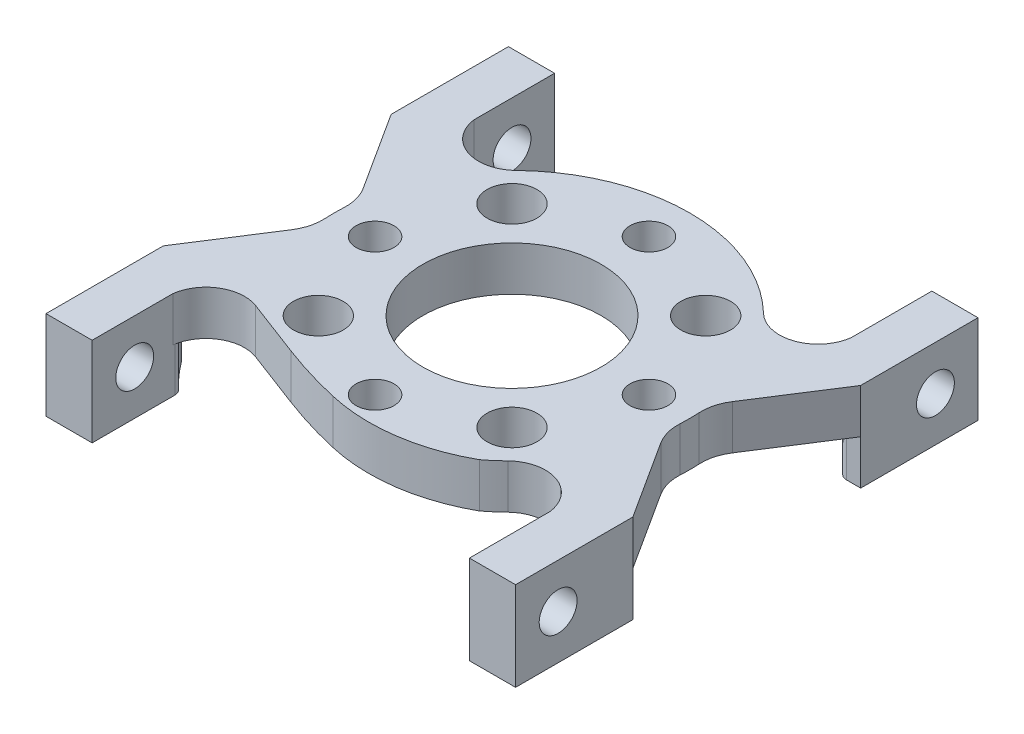
SolidWorks part; units mm, degrees
ref_plane "Front Plane" through (0, 0, 0) normal (0, 0, 1) x (1, 0, 0)
ref_plane "Top Plane" through (0, 0, 0) normal (0, 1, 0) x (1, 0, 0)
ref_plane "Right Plane" through (0, 0, 0) normal (1, 0, 0) x (0, 0, -1)
ref_plane "Plane1" through (0, 0, 0) normal (0, -1, 0) x (1, 0, 0)
sketch "Sketch1" plane through (0, 0, 0) normal (0, -1, 0) x (1, 0, 0)
  line L0 (16.764, 16.51) -> (-16.764, 16.51)
  line L1 (-16.764, 16.51) -> (-16.764, -16.51)
  line L2 (-16.764, -16.51) -> (16.764, -16.51)
  line L3 (16.764, -16.51) -> (16.764, 16.51)
extrude "Boss-Extrude1" add sketch "Sketch1" against normal blind 3.175
sketch "Sketch2" plane through (0, 3.175, 0) normal (0, 1, 0) x (-1, 0, 0)
  line L0 (-13.4696, 16.51) -> (-13.4696, 10.7533)
  line L1 (13.4696, 10.7533) -> (13.4696, 16.51)
  line L2 (13.4696, 16.51) -> (-13.4696, 16.51)
  arc A0 (-13.4696, 10.7533) -> (-8.8308, 9.1273) centre (-10.7425, 11.1033) ccw
  arc A1 (-8.8308, 9.1273) -> (8.8308, 9.1273) centre (0, 0) cw
  arc A2 (8.8308, 9.1273) -> (13.4696, 10.7533) centre (10.7425, 11.1033) ccw
extrude "Cut-Extrude1" cut sketch "Sketch2" against normal through all
sketch "Sketch3" plane through (0, 0, 0) normal (0, -1, 0) x (1, 0, 0)
  line L0 (-13.4696, 8.1331) -> (-16.764, 8.1331)
  line L1 (-16.764, 8.1331) -> (-16.764, 16.51)
  line L2 (-16.764, 16.51) -> (-13.4696, 16.51)
  line L3 (-13.4696, 16.51) -> (-13.4696, 8.1331)
extrude "Boss-Extrude2" add sketch "Sketch3" along normal blind 3.175
sketch "Sketch4" plane through (0, 3.175, 0) normal (0, 1, 0) x (-1, 0, 0)
  line L0 (-16.764, 8.1331) -> (-16.764, -8.1331)
  line L1 (-16.764, -8.1331) -> (-12.5937, -1.6399)
  line L2 (-12.5937, 1.6399) -> (-16.764, 8.1331)
  arc A0 (-12.5937, -1.6399) -> (-12.5937, 1.6399) centre (0, 0) cw
extrude "Cut-Extrude2" cut sketch "Sketch4" against normal through all
sketch "Sketch5" plane through (0, 0, 0) normal (0, -1, 0) x (1, 0, 0)
  line L0 (13.4696, 8.1331) -> (13.4696, 16.51)
  line L1 (13.4696, 16.51) -> (16.764, 16.51)
  line L2 (16.764, 16.51) -> (16.764, 8.1331)
  line L3 (16.764, 8.1331) -> (13.4696, 8.1331)
extrude "Boss-Extrude3" add sketch "Sketch5" along normal blind 3.175
sketch "Sketch6" plane through (0, 3.175, 0) normal (0, 1, 0) x (-1, 0, 0)
  line L0 (13.4696, -16.51) -> (13.4696, -10.7533)
  line L1 (-13.4696, -10.7533) -> (-13.4696, -16.51)
  line L2 (-13.4696, -16.51) -> (13.4696, -16.51)
  arc A0 (13.4696, -10.7533) -> (8.8308, -9.1273) centre (10.7425, -11.1033) ccw
  arc A1 (8.8308, -9.1273) -> (-8.8308, -9.1273) centre (0, 0) cw
  arc A2 (-8.8308, -9.1273) -> (-13.4696, -10.7533) centre (-10.7425, -11.1033) ccw
extrude "Cut-Extrude3" cut sketch "Sketch6" against normal through all
sketch "Sketch7" plane through (0, 0, 0) normal (0, -1, 0) x (1, 0, 0)
  line L0 (13.4696, -8.1331) -> (16.764, -8.1331)
  line L1 (16.764, -8.1331) -> (16.764, -16.51)
  line L2 (16.764, -16.51) -> (13.4696, -16.51)
  line L3 (13.4696, -16.51) -> (13.4696, -8.1331)
extrude "Boss-Extrude4" add sketch "Sketch7" along normal blind 3.175
sketch "Sketch8" plane through (0, 3.175, 0) normal (0, 1, 0) x (-1, 0, 0)
  line L0 (16.764, -8.1331) -> (16.764, 8.1331)
  line L1 (16.764, 8.1331) -> (12.5937, 1.6399)
  line L2 (12.5937, -1.6399) -> (16.764, -8.1331)
  arc A0 (12.5937, 1.6399) -> (12.5937, -1.6399) centre (0, 0) cw
extrude "Cut-Extrude4" cut sketch "Sketch8" against normal through all
sketch "Sketch9" plane through (0, 0, 0) normal (0, -1, 0) x (1, 0, 0)
  line L0 (-13.4696, -8.1331) -> (-13.4696, -16.51)
  line L1 (-13.4696, -16.51) -> (-16.764, -16.51)
  line L2 (-16.764, -16.51) -> (-16.764, -8.1331)
  line L3 (-16.764, -8.1331) -> (-13.4696, -8.1331)
extrude "Boss-Extrude5" add sketch "Sketch9" along normal blind 3.175
sketch "Sketch10" plane through (0, -3.175, 0) normal (0, -1, 0) x (1, 0, 0)
  line L0 (15.4224, -8.1331) -> (13.4696, -8.1331)
  line L1 (13.4696, -8.1331) -> (13.4696, -10.3293)
  arc A0 (13.4696, -10.3293) -> (15.4224, -8.1331) centre (4.064, 0) ccw
extrude "Cut-Extrude5" cut sketch "Sketch10" against normal blind 3.175
sketch "Sketch11" plane through (0, -3.175, 0) normal (0, -1, 0) x (1, 0, 0)
  line L0 (13.4696, 10.3293) -> (13.4696, 8.1331)
  line L1 (13.4696, 8.1331) -> (15.4224, 8.1331)
  arc A0 (15.4224, 8.1331) -> (13.4696, 10.3293) centre (4.064, 0) ccw
extrude "Cut-Extrude6" cut sketch "Sketch11" against normal blind 3.175
sketch "Sketch12" plane through (0, -3.175, 0) normal (0, -1, 0) x (1, 0, 0)
  line L0 (-15.4224, 8.1331) -> (-13.4696, 8.1331)
  line L1 (-13.4696, 8.1331) -> (-13.4696, 10.3293)
  arc A0 (-13.4696, 10.3293) -> (-15.4224, 8.1331) centre (-4.064, 0) ccw
extrude "Cut-Extrude7" cut sketch "Sketch12" against normal blind 3.175
sketch "Sketch13" plane through (0, -3.175, 0) normal (0, -1, 0) x (1, 0, 0)
  line L0 (-13.4696, -10.3293) -> (-13.4696, -8.1331)
  line L1 (-13.4696, -8.1331) -> (-15.4224, -8.1331)
  arc A0 (-15.4224, -8.1331) -> (-13.4696, -10.3293) centre (-4.064, 0) ccw
extrude "Cut-Extrude8" cut sketch "Sketch13" against normal blind 3.175
hole_wizard "Hole1" positions "Sketch15" profile "Sketch14" legacy
sketch "Sketch15" plane through (0, 0, 0) normal (0, -1, 0) x (-1, 0, 0)
  point P0 (0, 0)
sketch "Sketch14" plane through (0, 0, 0) normal (1, 0, 0) x (0, 0, -1)
  line L0 (0, 0) -> (0, 3.175)
  line L1 (0, 3.175) -> (6.3627, 3.175)
  line L2 (6.3627, 3.175) -> (6.3627, 0)
  line L3 (6.3627, 0) -> (0, 0)
  line L4 (0, 110) -> (0, -10) construction
  dimension "Diameter" = 12.7254
  dimension "Depth" = 3.175
hole_wizard "M2.5 Clearance Hole1" positions "Sketch17" profile "Sketch16" hole size "M2.5" standard "ANSI Metric"
sketch "Sketch17" plane through (0, 0, 0) normal (0, -1, 0) x (-1, 0, 0)
  point P0 (0, -9.779)
  point P1 (9.779, 0)
  point P2 (0, 9.779)
  point P3 (-9.779, 0)
sketch "Sketch16" plane through (0, 0, 9.779) normal (1, 0, 0) x (0, 0, -1)
  line L0 (0, 0) -> (0, 3.175)
  line L1 (0, 3.175) -> (1.3525, 3.175)
  line L2 (1.3525, 3.175) -> (1.3525, 0)
  line L5 (1.3525, 0) -> (0, 0)
  line L11 (0, -6.35) -> (0, 107.95) construction
  dimension "Thru Hole Dia." = 2.7051
  dimension "Thru Hole Depth" = 3.175
hole_wizard "M3 Clearance Hole1" positions "Sketch19" profile "Sketch18" hole size "M3" standard "ANSI Metric"
sketch "Sketch19" plane through (0, 0, 0) normal (0, -1, 0) x (-1, 0, 0)
  point P0 (6.9148, -6.9148)
  point P1 (6.9148, 6.9148)
  point P2 (-6.9148, 6.9148)
  point P3 (-6.9148, -6.9148)
sketch "Sketch18" plane through (-6.9148, 0, 6.9148) normal (1, 0, 0) x (0, 0, -1)
  line L0 (0, 0) -> (0, 3.175)
  line L1 (0, 3.175) -> (1.778, 3.175)
  line L2 (1.778, 3.175) -> (1.778, 0)
  line L5 (1.778, 0) -> (0, 0)
  line L11 (0, -6.35) -> (0, 107.95) construction
  dimension "Thru Hole Dia." = 3.556
  dimension "Thru Hole Depth" = 3.175
hole_wizard "M2.5 Clearance Hole2" positions "Sketch21" profile "Sketch20" hole size "M2.5" standard "ANSI Metric"
sketch "Sketch21" plane through (16.764, 0, 0) normal (1, 0, 0) x (0, 0, -1)
  point P0 (13.4704, 0)
sketch "Sketch20" plane through (16.764, 0, -13.4704) normal (0, 1, 0) x (0, 0, -1)
  line L0 (0, 0) -> (0, 3.2944)
  line L1 (0, 3.2944) -> (1.3525, 3.2944)
  line L2 (1.3525, 3.2944) -> (1.3525, 0)
  line L5 (1.3525, 0) -> (0, 0)
  line L11 (0, -6.35) -> (0, 107.95) construction
  dimension "Thru Hole Dia." = 2.7051
  dimension "Thru Hole Depth" = 3.2944
hole_wizard "M2.5 Clearance Hole3" positions "Sketch23" profile "Sketch22" hole size "M2.5" standard "ANSI Metric"
sketch "Sketch23" plane through (13.4696, 0, 0) normal (-1, 0, 0) x (0, 0, 1)
  point P0 (13.4704, 0)
sketch "Sketch22" plane through (13.4696, 0, 13.4704) normal (0, 1, 0) x (0, 0, 1)
  line L0 (0, 0) -> (0, 3.2944)
  line L1 (0, 3.2944) -> (1.3525, 3.2944)
  line L2 (1.3525, 3.2944) -> (1.3525, 0)
  line L5 (1.3525, 0) -> (0, 0)
  line L11 (0, -6.35) -> (0, 107.95) construction
  dimension "Thru Hole Dia." = 2.7051
  dimension "Thru Hole Depth" = 3.2944
hole_wizard "M2.5 Clearance Hole4" positions "Sketch25" profile "Sketch24" hole size "M2.5" standard "ANSI Metric"
sketch "Sketch25" plane through (-13.4696, 0, 0) normal (1, 0, 0) x (0, 0, -1)
  point P0 (-13.4704, 0)
  point P1 (13.4704, 0)
sketch "Sketch24" plane through (-13.4696, 0, 13.4704) normal (0, 1, 0) x (0, 0, -1)
  line L0 (0, 0) -> (0, 3.2944)
  line L1 (0, 3.2944) -> (1.3525, 3.2944)
  line L2 (1.3525, 3.2944) -> (1.3525, 0)
  line L5 (1.3525, 0) -> (0, 0)
  line L11 (0, -6.35) -> (0, 107.95) construction
  dimension "Thru Hole Dia." = 2.7051
  dimension "Thru Hole Depth" = 3.2944
fillet "Fillet1" radius 0.635 8 edges at (-13.4696, -1.5875, -10.3293) (-15.4224, -1.5875, 8.1331) (15.4224, -1.5875, -8.1331) (15.4224, -1.5875, 8.1331) (13.4696, -1.5875, -10.3293) (-13.4696, -1.5875, 10.3293) (-15.4224, -1.5875, -8.1331) (13.4696, -1.5875, 10.3293)
fillet "Fillet2" radius 3.175 4 edges at (-12.5937, 1.5875, -1.6399) (12.5937, 1.5875, -1.6399) (-12.5937, 1.5875, 1.6399) (12.5937, 1.5875, 1.6399)
sketch "Sketch26" plane through (0, 0, 0) normal (0, -1, 0) x (1, 0, 0)
  line L0 (-9.7674, 8.5326) -> (-5.7119, 10.0709)
  arc A0 (-13.4696, 10.7533) -> (-8.8308, 9.1273) centre (-10.7425, 11.1033) ccw construction
  arc A1 (-5.7119, 10.0709) -> (-1.406, 11.3748) centre (5.9417, -20.6515) cw
  arc A2 (-1.406, 11.3748) -> (7.7374, 10.0709) centre (1.4706, -1.1634) cw
  arc A3 (-9.7674, 8.5326) -> (-8.8308, 9.1273) centre (-10.7425, 11.1033) ccw
  arc A4 (7.7374, 10.0709) -> (-8.8308, 9.1273) centre (0, 0) ccw
  arc A5 (8.8308, 9.1273) -> (-8.8308, 9.1273) centre (0, 0) ccw construction
extrude "Cut-Extrude9" cut sketch "Sketch26" against normal up to next
sketch "Sketch29" plane through (0, 0, 0) normal (0, -1, 0) x (1, 0, 0)
  line L0 (-2.0054, -11.3072) -> (1.7265, -11.3072) construction
ref_plane "Plane2" through (0, -5.0278, -3.0682) normal (0, -0.8536, -0.5209) x (-1, 0, 0)
sketch "Sketch30" plane through (0, -5.0278, -3.0682) normal (0, -0.8536, -0.5209) x (-1, 0, 0)
  line L1 (-6.9394, 18.9824) -> (7.5098, 18.9824)
  line L2 (-6.9394, 18.9824) -> (-6.9394, 9.1912)
  line L3 (-6.9394, 9.1912) -> (7.5098, 9.1912)
  line L4 (7.5098, 18.9824) -> (7.5098, 9.1912)
extrude "Cut-Extrude12" cut sketch "Sketch30" along normal up to next
